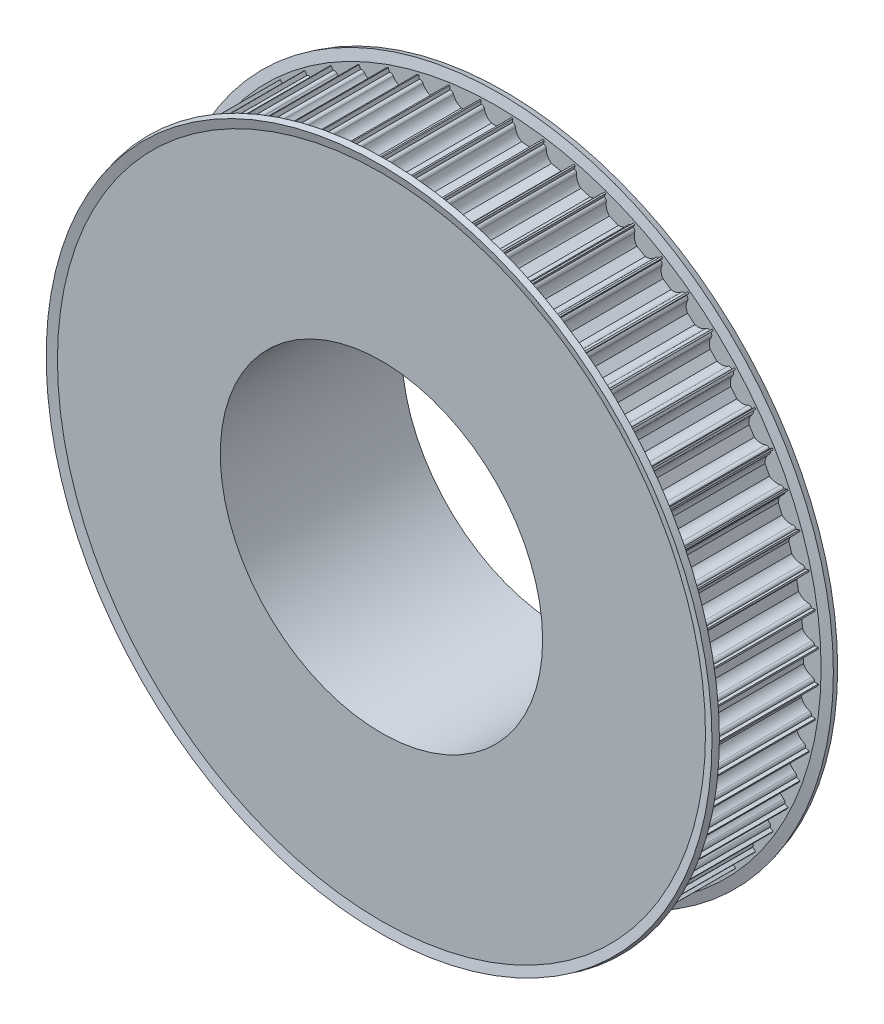
SolidWorks part; units mm, degrees
ref_plane "Front Plane" through (0, 0, 0) normal (0, 0, 1) x (1, 0, 0)
ref_plane "Top Plane" through (0, 0, 0) normal (0, 1, 0) x (1, 0, 0)
ref_plane "Right Plane" through (0, 0, 0) normal (1, 0, 0) x (0, 0, -1)
sketch "Sketch1" plane through (0, 0, 0) normal (1, 0, 0) x (0, 0, -1)
  line L0 (0, 0) -> (34.4325, 0) construction
  line L1 (0, 40) -> (45, 40)
  line L2 (45, 40) -> (45, 55.5)
  line L3 (45, 55.5) -> (30, 55.5)
  line L4 (30, 55.5) -> (30, 80)
  line L5 (30, 80) -> (0, 80)
  line L6 (0, 80) -> (0, 40)
  dimension "D1" = 80
  dimension "D2" = 40
  dimension "D3" = 30
  dimension "D4" = 15
  dimension "D5" = 15.5
revolve "Revolve1" add sketch "Sketch1" angle 360 about L0
sketch "Sketch2" plane through (0, 0, 0) normal (0, 0, 1) x (1, 0, 0)
  line L0 (-3.6742, 79) -> (-3.75, 79)
  line L1 (-3.75, 79) -> (-3.75, 81)
  line L2 (-3.75, 81) -> (3.75, 81)
  line L3 (3.75, 81) -> (3.75, 79)
  line L4 (3.75, 79) -> (3.6742, 79)
  line L5 (-1.199, 76.25) -> (1.199, 76.25)
  arc A0 (2.9394, 78.4) -> (1.199, 76.25) centre (0, 79) cw
  arc A1 (2.9394, 78.4) -> (3.6742, 79) centre (3.6742, 78.25) cw
  arc A2 (-2.9394, 78.4) -> (-3.6742, 79) centre (-3.6742, 78.25) ccw
  arc A3 (-1.199, 76.25) -> (-2.9394, 78.4) centre (0, 79) cw
  point P11 (3, 79)
  point P14 (-3, 79)
  dimension "D1" = 3
  dimension "D3" = 7.5
  dimension "D6" = 0.75
  dimension "D2" = 79
  dimension "D4" = 2
  dimension "D5" = 0.75
  dimension "D7" = 2.75
extrude "Cut-Extrude1" cut sketch "Sketch2" against normal up to next (30 mm away)
pattern_circular "CirPattern1" count 64 over 360 about axis through (0, 0, 0) along (0, 0, 1) of "Cut-Extrude1"
sketch "Sketch3" plane through (0, 0, 0) normal (1, 0, 0) x (0, 0, -1)
  line L0 (15, -40.9775) -> (15, -10.6098) construction
  line L1 (30, -40.9775) -> (0, -40.9775) construction
  line L2 (30, -10.6098) -> (0, -10.6098) construction
  line L3 (30, 55.5) -> (30, 80.4125)
  line L4 (30, 80.4125) -> (30.592, 82.6218)
  line L5 (30.592, 82.6218) -> (29.1431, 83.01)
  line L6 (29.1431, 83.01) -> (28.5, 80.61)
  line L7 (28.5, 80.61) -> (28.5, 55.5)
  line L8 (28.5, 55.5) -> (30, 55.5)
  line L9 (1.5, 55.5) -> (0, 55.5)
  line L10 (1.5, 80.61) -> (1.5, 55.5)
  line L11 (-0.592, 82.6218) -> (0.8569, 83.01)
  line L12 (0, 80.4125) -> (-0.592, 82.6218)
  line L13 (0, 55.5) -> (0, 80.4125)
  line L14 (0.8569, 83.01) -> (1.5, 80.61)
  line L15 (0, 0) -> (30, 0) construction
  line L16 (30, -55.5) -> (30, 55.5) construction
  dimension "D1" = 15
  dimension "D2" = 1.5
  dimension "D3" = 25.11
  dimension "D4" = 2.4
revolve "Revolve2" add sketch "Sketch3" angle 360 about L15
